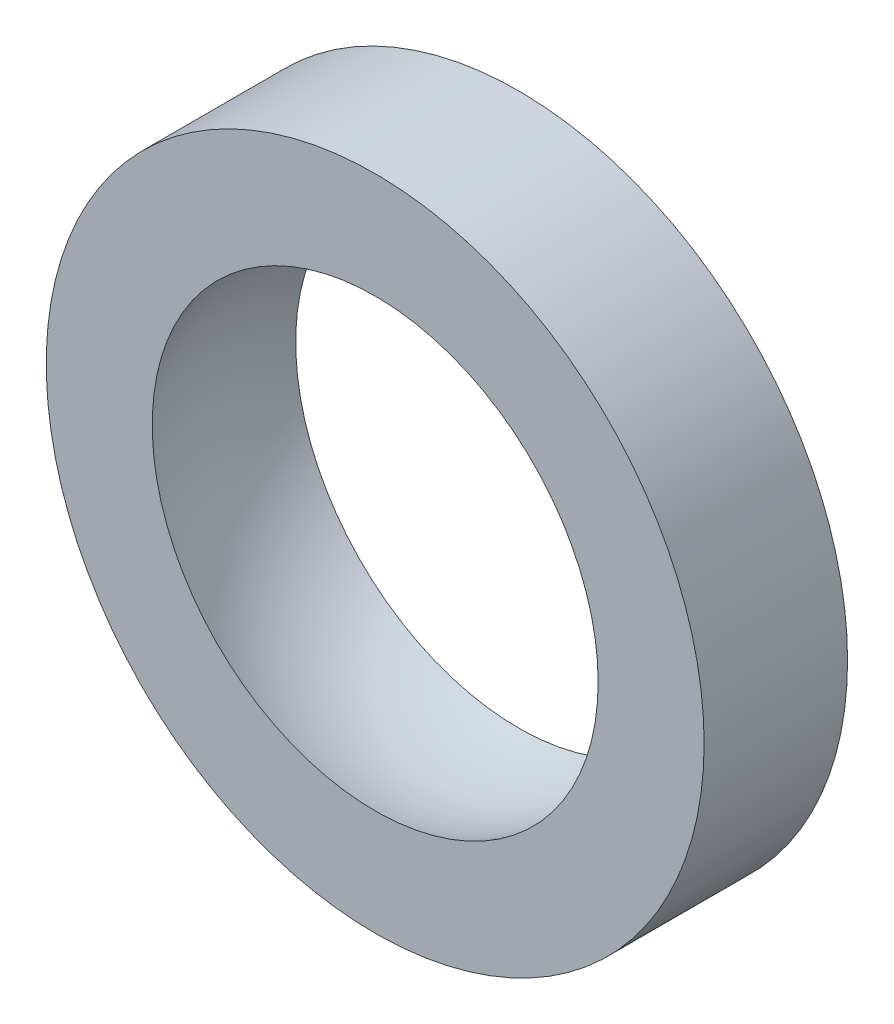
SolidWorks part; units mm, degrees
material "Default"
ref_plane "Top" through (0, 0, 0) normal (0, 0, 1) x (1, 0, 0)
ref_plane "Right" through (0, 0, 0) normal (0, 1, 0) x (1, 0, 0)
ref_plane "Front" through (0, 0, 0) normal (1, 0, 0) x (0, 0, -1)
sketch "Sketch1" plane through (0, 0, 0) normal (1, 0, 0) x (0, 0, -1)
  line L0 (-1.4583, -4.5337) -> (-1.4583, -6.6886)
  line L1 (-1.4583, -6.6886) -> (1.4583, -6.6886)
  line L2 (1.4583, -6.6886) -> (1.4583, -4.5337)
  line L3 (-15.3143, 0) -> (15.3143, 0) construction
  arc A0 (-1.4583, -4.5337) -> (1.4583, -4.5337) centre (0, 0) ccw
  point P10 (0, 0)
  dimension "D1" = 4.7625
revolve "Revolve1" add sketch "Sketch1" angle 360 about L3
